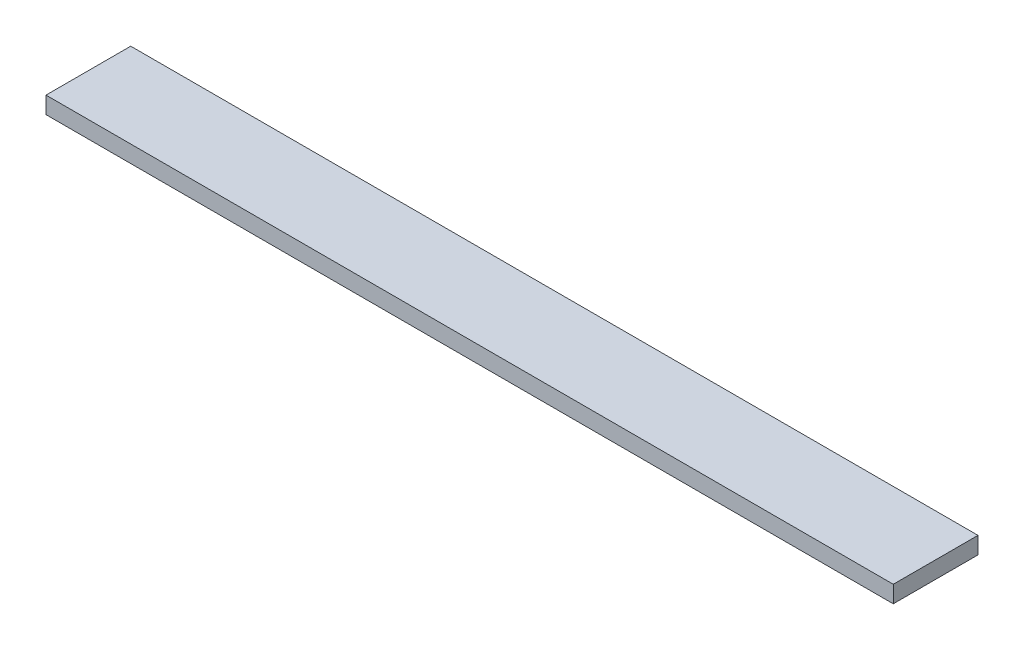
SolidWorks part; units mm, degrees
ref_plane "Спереди" through (0, 0, 0) normal (0, 0, 1) x (1, 0, 0)
ref_plane "Сверху" through (0, 0, 0) normal (0, 1, 0) x (1, 0, 0)
ref_plane "Справа" through (0, 0, 0) normal (1, 0, 0) x (0, 0, -1)
sketch "Эскиз1" plane through (0, 0, 0) normal (1, 0, 0) x (0, 0, -1)
  line L1 (0, 0) -> (20, 0)
  line L2 (0, 0) -> (0, 4)
  line L3 (0, 4) -> (20, 4)
  line L4 (20, 0) -> (20, 4)
extrude "Бобышка-Вытянуть1" add sketch "Эскиз1" along normal blind 200
